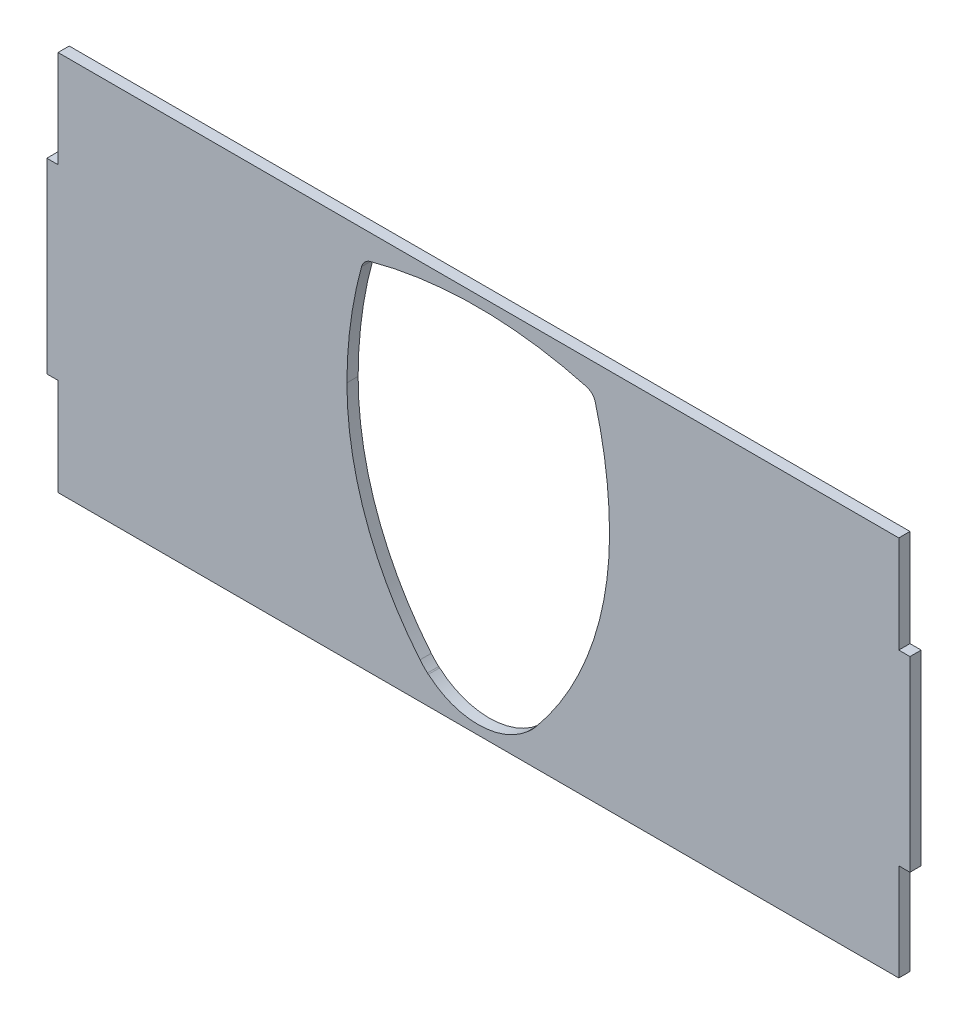
SolidWorks part; units mm, degrees
ref_plane "Front Plane" through (0, 0, 0) normal (0, 0, 1) x (1, 0, 0)
ref_plane "Top Plane" through (0, 0, 0) normal (0, 1, 0) x (1, 0, 0)
ref_plane "Right Plane" through (0, 0, 0) normal (1, 0, 0) x (0, 0, -1)
sketch "Sketch1" plane through (0, 0, 0) normal (0, 0, 1) x (1, 0, 0)
  line L0 (-112.3427, 49.5841) -> (-112.3427, 23.5841)
  line L1 (-112.3427, -52.4159) -> (112.6573, -52.4159)
  line L2 (112.6573, -52.4159) -> (112.6573, -26.4159)
  line L3 (112.6573, 49.5841) -> (-112.3427, 49.5841)
  line L4 (13.2743, -45.0088) -> (13.3019, -45.032)
  line L5 (-13.2467, -44.992) -> (-13.2191, -44.9689)
  line L6 (-112.3427, 23.5841) -> (-115.3427, 23.5841)
  line L7 (-115.3427, 23.5841) -> (-115.3427, -26.4159)
  line L8 (-115.3427, -26.4159) -> (-112.3427, -26.4159)
  line L9 (-112.3427, -26.4159) -> (-112.3427, -52.4159)
  line L10 (112.6573, -26.4159) -> (115.6573, -26.4159)
  line L11 (115.6573, -26.4159) -> (115.6573, 23.5841)
  line L12 (115.6573, 23.5841) -> (112.6573, 23.5841)
  line L13 (112.6573, 23.5841) -> (112.6573, 49.5841)
  arc A0 (31.4274, 40.4713) -> (29.0522, 42.8536) centre (28.1552, 39.5841) ccw
  arc A1 (35.2533, 11.5734) -> (31.4274, 40.4713) centre (-74.5453, 11.739) ccw
  arc A2 (15.517, -42.7739) -> (35.2533, 11.5734) centre (-49.7953, 11.7017) ccw
  arc A3 (13.5335, -44.8349) -> (15.517, -42.7739) centre (0.0504, -29.8736) ccw
  arc A4 (-13.2191, -44.9689) -> (13.2743, -45.0088) centre (0.0504, -29.8736) ccw
  arc A5 (-15.455, -42.7272) -> (-13.4777, -44.7941) centre (0.0504, -29.8736) ccw
  arc A6 (-35.0273, 11.6794) -> (-15.455, -42.7272) centre (50.0213, 11.5511) ccw
  arc A7 (-31.1143, 40.5656) -> (-35.0273, 11.6794) centre (74.7712, 11.5138) ccw
  arc A8 (-28.7319, 42.9408) -> (-31.1143, 40.5656) centre (-27.8447, 39.6686) ccw
  arc A9 (29.0522, 42.8536) -> (-28.7319, 42.9408) centre (0.0004, -63.0319) ccw
  spline S0 degree 3 poles (13.3019, -45.032) (13.3024, -45.0319) (13.3036, -45.0316) (13.3103, -45.0268) (13.3274, -45.0136) (13.3684, -44.9798) (13.4323, -44.9247) (13.4892, -44.8745) (13.5187, -44.8481) (13.5335, -44.8349) knots 0 0 0 0 0.083775 0.166803 0.250583 0.499711 0.748904 0.874548 1 1 1 1
  spline S1 degree 3 poles (-13.4777, -44.7941) (-13.468, -44.803) (-13.4484, -44.8206) (-13.4195, -44.8465) (-13.3729, -44.8877) (-13.3132, -44.9395) (-13.2697, -44.9755) (-13.2502, -44.9906) (-13.2479, -44.9915) (-13.2467, -44.992) knots 0 0 0 0 0.083818 0.166849 0.250508 0.499664 0.748829 0.874626 1 1 1 1
  dimension "D1" = 225
  dimension "D2" = 102
  dimension "D3" = 3
  dimension "D4" = 112.3427
  dimension "D5" = 50
  dimension "D6" = 26
  dimension "D7" = 52.4159
  dimension "D8" = 3
  dimension "D9" = 26
  dimension "D10" = 50
extrude "Boss-Extrude1" add sketch "Sketch1" along normal blind 3
